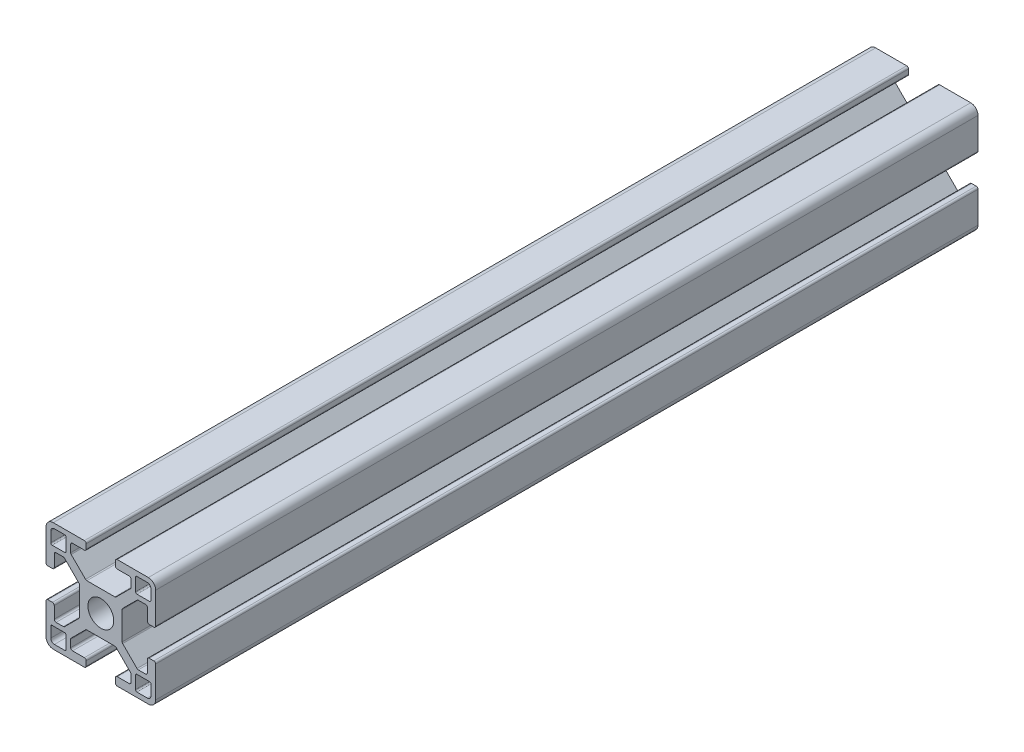
SolidWorks part; units mm, degrees
ref_plane "Front Plane" through (0, 0, 0) normal (0, 0, 1) x (1, 0, 0)
ref_plane "Top Plane" through (0, 0, 0) normal (0, 1, 0) x (1, 0, 0)
ref_plane "Right Plane" through (0, 0, 0) normal (1, 0, 0) x (0, 0, -1)
sketch "Sketch1" plane through (0, 0, 0) normal (0, 0, 1) x (1, 0, 0)
  line L0 (3.9799, -2.4733) -> (3.1981, -1.4942) construction
  line L1 (1.4942, -3.1981) -> (2.4733, -3.9799) construction
  line L2 (-2.4733, -3.9799) -> (-1.4942, -3.1981) construction
  line L3 (-3.1981, -1.4942) -> (-3.9799, -2.4733) construction
  line L4 (-3.9799, 2.4733) -> (-3.1981, 1.4942) construction
  line L5 (-1.4942, 3.1981) -> (-2.4733, 3.9799) construction
  line L6 (2.4733, 3.9799) -> (1.4942, 3.1981) construction
  line L7 (3.1981, 1.4942) -> (3.9799, 2.4733) construction
  line L8 (-12.6999, -13.6999) -> (-9.881, -13.6999)
  line L9 (-13.6999, -9.881) -> (-13.6999, -12.6999)
  line L10 (-9.88, -9.5) -> (-13.3189, -9.5)
  line L11 (-9.5, -13.3189) -> (-9.5, -9.88)
  line L12 (13.6999, -12.6999) -> (13.6999, -9.881)
  line L13 (9.881, -13.6999) -> (12.6999, -13.6999)
  line L14 (9.5, -9.88) -> (9.5, -13.3189)
  line L15 (13.3189, -9.5) -> (9.88, -9.5)
  line L16 (9.88, 9.5) -> (13.3189, 9.5)
  line L17 (9.5, 13.3189) -> (9.5, 9.88)
  line L18 (12.6999, 13.6999) -> (9.881, 13.6999)
  line L19 (13.6999, 9.881) -> (13.6999, 12.6999)
  line L20 (-13.6999, 12.6999) -> (-13.6999, 9.881)
  line L21 (-9.881, 13.6999) -> (-12.6999, 13.6999)
  line L22 (-9.5, 9.88) -> (-9.5, 13.3189)
  line L23 (-13.3189, 9.5) -> (-9.88, 9.5)
  line L24 (14.4999, -4) -> (13.2425, -4)
  line L25 (12.7425, -4.5) -> (12.7425, -7.7325)
  line L26 (12.2428, -8.25) -> (10.2602, -8.25)
  line L27 (9.9066, -8.1035) -> (5.9811, -4.178)
  line L28 (5.8347, -3.8245) -> (5.8347, -1.0125)
  line L29 (5.8347, -1.0125) -> (5.3247, -0.0625) construction
  line L30 (5.3247, -0.0625) -> (5.8347, 0.8875) construction
  line L31 (5.8347, 0.8875) -> (5.8347, 3.8245)
  line L32 (5.9811, 4.178) -> (9.9066, 8.1035)
  line L33 (10.2602, 8.25) -> (12.2428, 8.25)
  line L34 (12.7425, 7.7325) -> (12.7425, 4.5)
  line L35 (13.2425, 4) -> (14.4999, 4)
  line L36 (14.9999, 4.5) -> (14.9999, 12.9999)
  line L37 (12.9999, 14.9999) -> (4.5, 14.9999)
  line L38 (4, 14.4999) -> (4, 13.2425)
  line L39 (4.5, 12.7425) -> (7.7325, 12.7425)
  line L40 (8.25, 12.2428) -> (8.25, 10.2602)
  line L41 (8.1035, 9.9066) -> (4.178, 5.9811)
  line L42 (3.8245, 5.8347) -> (0.95, 5.8347)
  line L43 (0.95, 5.8347) -> (0, 5.3247) construction
  line L44 (0, 5.3247) -> (-0.95, 5.8347) construction
  line L45 (-0.95, 5.8347) -> (-3.8245, 5.8347)
  line L46 (-4.178, 5.9811) -> (-8.1035, 9.9066)
  line L47 (-8.25, 10.2602) -> (-8.25, 12.2428)
  line L48 (-7.7325, 12.7425) -> (-4.5, 12.7425)
  line L49 (-4, 13.2425) -> (-4, 14.4999)
  line L50 (-4.5, 14.9999) -> (-12.9999, 14.9999)
  line L51 (-14.9999, 12.9999) -> (-14.9999, 4.5)
  line L52 (-14.4999, 4) -> (-13.2425, 4)
  line L53 (-12.7425, 4.5) -> (-12.7425, 7.7325)
  line L54 (-12.2428, 8.25) -> (-10.2602, 8.25)
  line L55 (-9.9066, 8.1035) -> (-5.9811, 4.178)
  line L56 (-5.8347, 3.8245) -> (-5.8347, 0.8875)
  line L57 (-5.8347, 0.8875) -> (-5.3247, -0.0625) construction
  line L58 (-5.3247, -0.0625) -> (-5.8347, -1.0125) construction
  line L59 (-5.8347, -1.0125) -> (-5.8347, -3.8245)
  line L60 (-5.9811, -4.178) -> (-9.9066, -8.1035)
  line L61 (-10.2602, -8.25) -> (-12.2428, -8.25)
  line L62 (-12.7425, -7.7325) -> (-12.7425, -4.5)
  line L63 (-13.2425, -4) -> (-14.4999, -4)
  line L64 (-14.9999, -4.5) -> (-14.9999, -12.9999)
  line L65 (-12.9999, -14.9999) -> (-4.5, -14.9999)
  line L66 (-4, -14.4999) -> (-4, -13.2425)
  line L67 (-4.5, -12.7425) -> (-7.7325, -12.7425)
  line L68 (-8.25, -12.2428) -> (-8.25, -10.2602)
  line L69 (-8.1035, -9.9066) -> (-4.178, -5.9811)
  line L70 (-3.8245, -5.8347) -> (-0.95, -5.8347)
  line L71 (-0.95, -5.8347) -> (0, -5.3247) construction
  line L72 (0, -5.3247) -> (0.95, -5.8347) construction
  line L73 (0.95, -5.8347) -> (3.8245, -5.8347)
  line L74 (4.178, -5.9811) -> (8.1035, -9.9066)
  line L75 (8.25, -10.2602) -> (8.25, -12.2428)
  line L76 (7.7325, -12.7425) -> (4.5, -12.7425)
  line L77 (4, -13.2425) -> (4, -14.4999)
  line L78 (4.5, -14.9999) -> (12.9999, -14.9999)
  line L79 (14.9999, -12.9999) -> (14.9999, -4.5)
  line L80 (-5.8347, -1.0125) -> (-5.8347, 0.8875)
  line L81 (-0.95, 5.8347) -> (0.95, 5.8347)
  line L82 (5.8347, 0.8875) -> (5.8347, -1.0125)
  line L83 (-0.95, -5.8347) -> (0.95, -5.8347)
  arc A0 (2.4733, -3.9799) -> (3.9799, -2.4733) centre (3.1422, -3.1422) ccw construction
  arc A1 (-1.4942, -3.1981) -> (1.4942, -3.1981) centre (0, 0) ccw construction
  arc A2 (-3.9799, -2.4733) -> (-2.4733, -3.9799) centre (-3.1422, -3.1422) ccw construction
  arc A3 (-3.1981, 1.4942) -> (-3.1981, -1.4942) centre (0, 0) ccw construction
  arc A4 (-2.4733, 3.9799) -> (-3.9799, 2.4733) centre (-3.1422, 3.1422) ccw construction
  arc A5 (1.4942, 3.1981) -> (-1.4942, 3.1981) centre (0, 0) ccw construction
  arc A6 (3.9799, 2.4733) -> (2.4733, 3.9799) centre (3.1422, 3.1422) ccw construction
  arc A7 (3.1981, -1.4942) -> (3.1981, 1.4942) centre (0, 0) ccw construction
  arc A8 (-13.6999, -12.6999) -> (-12.6999, -13.6999) centre (-12.6999, -12.6999) ccw
  arc A9 (-13.3189, -9.5) -> (-13.6999, -9.881) centre (-13.3189, -9.881) ccw
  arc A10 (-9.5, -9.88) -> (-9.88, -9.5) centre (-9.88, -9.88) ccw
  arc A11 (-9.881, -13.6999) -> (-9.5, -13.3189) centre (-9.881, -13.3189) ccw
  arc A12 (12.6999, -13.6999) -> (13.6999, -12.6999) centre (12.6999, -12.6999) ccw
  arc A13 (9.5, -13.3189) -> (9.881, -13.6999) centre (9.881, -13.3189) ccw
  arc A14 (9.88, -9.5) -> (9.5, -9.88) centre (9.88, -9.88) ccw
  arc A15 (13.6999, -9.881) -> (13.3189, -9.5) centre (13.3189, -9.881) ccw
  arc A16 (9.5, 9.88) -> (9.88, 9.5) centre (9.88, 9.88) ccw
  arc A17 (9.881, 13.6999) -> (9.5, 13.3189) centre (9.881, 13.3189) ccw
  arc A18 (13.6999, 12.6999) -> (12.6999, 13.6999) centre (12.6999, 12.6999) ccw
  arc A19 (13.3189, 9.5) -> (13.6999, 9.881) centre (13.3189, 9.881) ccw
  arc A20 (14.9999, -4.5) -> (14.4999, -4) centre (14.4999, -4.5) ccw
  arc A21 (13.2425, -4) -> (12.7425, -4.5) centre (13.2425, -4.5) ccw
  arc A22 (12.2428, -8.25) -> (12.7425, -7.7325) centre (12.2428, -7.75) ccw
  arc A23 (9.9066, -8.1035) -> (10.2602, -8.25) centre (10.2602, -7.75) ccw
  arc A24 (5.8347, -3.8245) -> (5.9811, -4.178) centre (6.3347, -3.8245) ccw
  arc A25 (5.9811, 4.178) -> (5.8347, 3.8245) centre (6.3347, 3.8245) ccw
  arc A26 (10.2602, 8.25) -> (9.9066, 8.1035) centre (10.2602, 7.75) ccw
  arc A27 (12.7425, 7.7325) -> (12.2428, 8.25) centre (12.2428, 7.75) ccw
  arc A28 (12.7425, 4.5) -> (13.2425, 4) centre (13.2425, 4.5) ccw
  arc A29 (14.4999, 4) -> (14.9999, 4.5) centre (14.4999, 4.5) ccw
  arc A30 (14.9999, 12.9999) -> (12.9999, 14.9999) centre (12.9999, 12.9999) ccw
  arc A31 (4.5, 14.9999) -> (4, 14.4999) centre (4.5, 14.4999) ccw
  arc A32 (4, 13.2425) -> (4.5, 12.7425) centre (4.5, 13.2425) ccw
  arc A33 (8.25, 12.2428) -> (7.7325, 12.7425) centre (7.75, 12.2428) ccw
  arc A34 (8.1035, 9.9066) -> (8.25, 10.2602) centre (7.75, 10.2602) ccw
  arc A35 (3.8245, 5.8347) -> (4.178, 5.9811) centre (3.8245, 6.3347) ccw
  arc A36 (-4.178, 5.9811) -> (-3.8245, 5.8347) centre (-3.8245, 6.3347) ccw
  arc A37 (-8.25, 10.2602) -> (-8.1035, 9.9066) centre (-7.75, 10.2602) ccw
  arc A38 (-7.7325, 12.7425) -> (-8.25, 12.2428) centre (-7.75, 12.2428) ccw
  arc A39 (-4.5, 12.7425) -> (-4, 13.2425) centre (-4.5, 13.2425) ccw
  arc A40 (-4, 14.4999) -> (-4.5, 14.9999) centre (-4.5, 14.4999) ccw
  arc A41 (-12.9999, 14.9999) -> (-14.9999, 12.9999) centre (-12.9999, 12.9999) ccw
  arc A42 (-14.9999, 4.5) -> (-14.4999, 4) centre (-14.4999, 4.5) ccw
  arc A43 (-13.2425, 4) -> (-12.7425, 4.5) centre (-13.2425, 4.5) ccw
  arc A44 (-12.2428, 8.25) -> (-12.7425, 7.7325) centre (-12.2428, 7.75) ccw
  arc A45 (-9.9066, 8.1035) -> (-10.2602, 8.25) centre (-10.2602, 7.75) ccw
  arc A46 (-5.8347, 3.8245) -> (-5.9811, 4.178) centre (-6.3347, 3.8245) ccw
  arc A47 (-5.9811, -4.178) -> (-5.8347, -3.8245) centre (-6.3347, -3.8245) ccw
  arc A48 (-10.2602, -8.25) -> (-9.9066, -8.1035) centre (-10.2602, -7.75) ccw
  arc A49 (-12.7425, -7.7325) -> (-12.2428, -8.25) centre (-12.2428, -7.75) ccw
  arc A50 (-12.7425, -4.5) -> (-13.2425, -4) centre (-13.2425, -4.5) ccw
  arc A51 (-14.4999, -4) -> (-14.9999, -4.5) centre (-14.4999, -4.5) ccw
  arc A52 (-14.9999, -12.9999) -> (-12.9999, -14.9999) centre (-12.9999, -12.9999) ccw
  arc A53 (-4.5, -14.9999) -> (-4, -14.4999) centre (-4.5, -14.4999) ccw
  arc A54 (-4, -13.2425) -> (-4.5, -12.7425) centre (-4.5, -13.2425) ccw
  arc A55 (-8.25, -12.2428) -> (-7.7325, -12.7425) centre (-7.75, -12.2428) ccw
  arc A56 (-8.1035, -9.9066) -> (-8.25, -10.2602) centre (-7.75, -10.2602) ccw
  arc A57 (-3.8245, -5.8347) -> (-4.178, -5.9811) centre (-3.8245, -6.3347) ccw
  arc A58 (4.178, -5.9811) -> (3.8245, -5.8347) centre (3.8245, -6.3347) ccw
  arc A59 (8.25, -10.2602) -> (8.1035, -9.9066) centre (7.75, -10.2602) ccw
  arc A60 (7.7325, -12.7425) -> (8.25, -12.2428) centre (7.75, -12.2428) ccw
  arc A61 (4.5, -12.7425) -> (4, -13.2425) centre (4.5, -13.2425) ccw
  arc A62 (4, -14.4999) -> (4.5, -14.9999) centre (4.5, -14.4999) ccw
  arc A63 (12.9999, -14.9999) -> (14.9999, -12.9999) centre (12.9999, -12.9999) ccw
  arc A64 (-12.6999, 13.6999) -> (-13.6999, 12.6999) centre (-12.6999, 12.6999) ccw
  arc A65 (-9.5, 13.3189) -> (-9.881, 13.6999) centre (-9.881, 13.3189) ccw
  arc A66 (-9.88, 9.5) -> (-9.5, 9.88) centre (-9.88, 9.88) ccw
  arc A67 (-13.6999, 9.881) -> (-13.3189, 9.5) centre (-13.3189, 9.881) ccw
  circle A68 centre (0, 0) radius 3.53
extrude "Boss-Extrude1" add sketch "Sketch1" along normal mid plane 225
